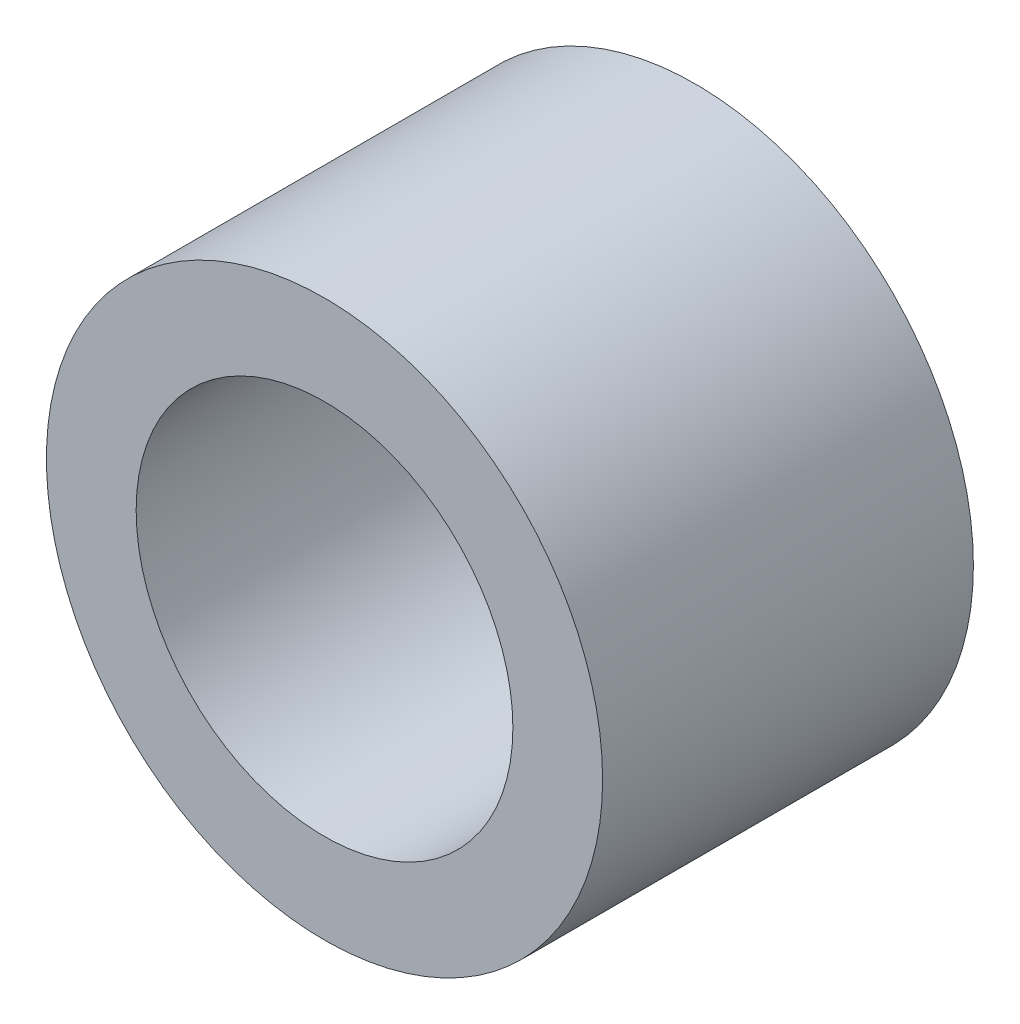
SolidWorks part; units mm, degrees
material "Delrin 2700 NC010, Low Viscosity Acetal Copolymer (SS)"
ref_plane "Front Plane" through (0, 0, 0) normal (0, 0, 1) x (1, 0, 0)
ref_plane "Top Plane" through (0, 0, 0) normal (0, 1, 0) x (1, 0, 0)
ref_plane "Right Plane" through (0, 0, 0) normal (1, 0, 0) x (0, 0, -1)
sketch "Sketch1" plane through (0, 0, 0) normal (0, 0, 1) x (1, 0, 0)
  circle A0 centre (0, 0) radius 4.7625
  circle A1 centre (0, 0) radius 3.2258
  dimension "D1" = 9.525
  dimension "ID" = 6.4516
extrude "Extrude1" add sketch "Sketch1" along normal mid plane 6.35
sketch "Sketch2" plane through (0, 0, 0) normal (1, 0, 0) x (0, 0, -1)
  line L0 (-3.175, -3.2258) -> (3.175, -3.2258) construction
  line L3 (3.175, 3.2258) -> (-3.175, 3.2258) construction
  line L5 (-3.175, -3.2258) -> (3.175, -3.2258)
  line L6 (3.175, 3.2258) -> (-3.175, 3.2258)
sketch "Sketch4" plane through (0, 0, 3.175) normal (0, 0, 1) x (1, 0, 0)
  line L0 (0, 0) -> (-2.281, 2.281)
  line L1 (0, -6.985) -> (0, 6.985) construction
  circle A0 centre (0, 0) radius 3.2258 construction
  dimension "D1" = 45
